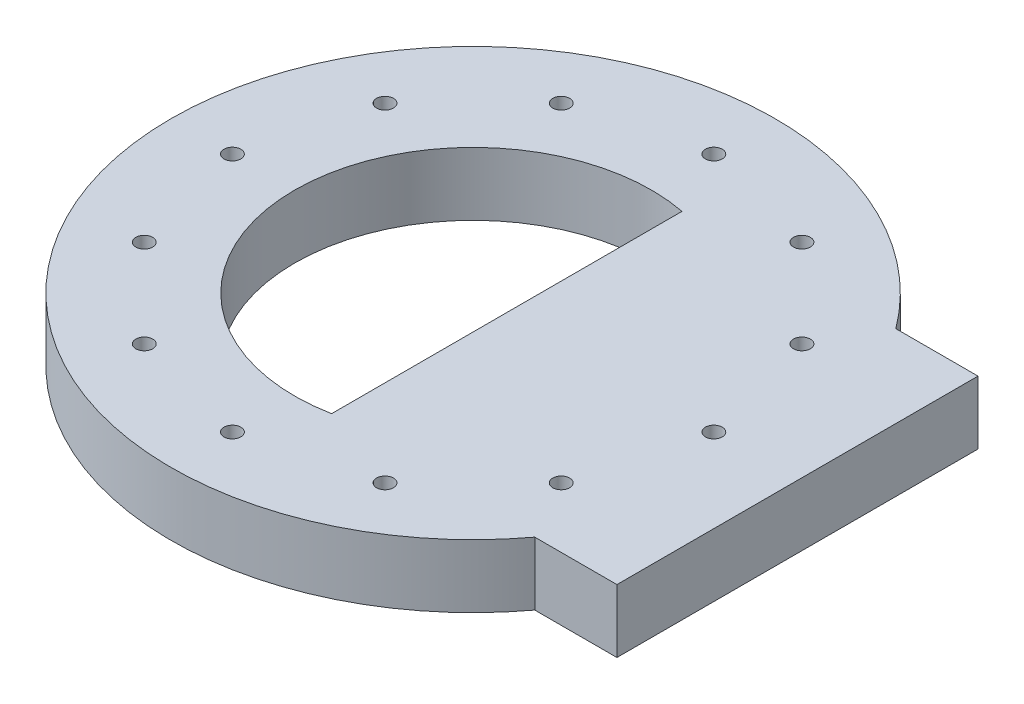
SolidWorks part; units mm, degrees
ref_plane "Front Plane" through (0, 0, 0) normal (0, 0, 1) x (1, 0, 0)
ref_plane "Top Plane" through (0, 0, 0) normal (0, 1, 0) x (1, 0, 0)
ref_plane "Right Plane" through (0, 0, 0) normal (1, 0, 0) x (0, 0, -1)
sketch "Sketch1" plane through (0, 0, 0) normal (0, 1, 0) x (1, 0, 0)
  circle A0 centre (0, 0) radius 101.6 construction
  circle A1 centre (0, 0) radius 127.508
  circle A2 centre (0, 0) radius 75.311
  circle A3 centre (0, 101.6) radius 3.5687
  circle A4 centre (50.8, 87.9882) radius 3.5687
  circle A5 centre (87.9882, 50.8) radius 3.5687
  circle A6 centre (101.6, 0) radius 3.5687
  circle A7 centre (87.9882, -50.8) radius 3.5687
  circle A8 centre (50.8, -87.9882) radius 3.5687
  circle A9 centre (0, -101.6) radius 3.5687
  circle A10 centre (-50.8, -87.9882) radius 3.5687
  circle A11 centre (-87.9882, -50.8) radius 3.5687
  circle A12 centre (-101.6, 0) radius 3.5687
  circle A13 centre (-87.9882, 50.8) radius 3.5687
  circle A14 centre (-50.8, 87.9882) radius 3.5687
  point P31 (0, 0)
  dimension "D1" = 203.2
  dimension "D2" = 255.016
  dimension "D4" = 7.1374
  dimension "D3" = 150.622
  dimension "D5" = 12
extrude "Boss-Extrude1" add sketch "Sketch1" along normal blind 26.67
sketch "Sketch2" plane through (0, 26.67, 0) normal (0, 1, 0) x (1, 0, 0)
  line L0 (14.224, 73.9556) -> (14.224, -73.9556)
  line L1 (136.906, 76.2) -> (136.906, -76.2)
  line L2 (136.906, 76.2) -> (102.2343, 76.2)
  line L3 (136.906, -76.2) -> (102.2343, -76.2)
  circle A0 centre (0, 0) radius 75.311 construction
  arc A1 (14.224, 73.9556) -> (14.224, -73.9556) centre (0, 0) cw
  circle A2 centre (0, 0) radius 127.508 construction
  arc A3 (102.2343, 76.2) -> (102.2343, -76.2) centre (0, 0) cw
  point P11 (136.906, 0)
  dimension "D1" = 14.224
  dimension "D2" = 136.906
  dimension "D3" = 152.4
extrude "Boss-Extrude2" add sketch "Sketch2" against normal through all
equation "\"A\"= 10.04in"
equation "\"B\"= 7in"
equation "\"C\"= 5.93in"
equation "\"D\"= .56in"
equation "\"E\"= 5.39in"
equation "\"F\"= 1.03in"
equation "\"D2@Sketch1\"=\"A\""
equation "\"BC\"=203.2"
equation "\"D1@Sketch1\"=\"BC\""
equation "\"diam_mount_hole\"=7.1374"
equation "\"D4@Sketch1\"=\"diam_mount_hole\""
equation "\"thick\"= 2.1in / 2"
equation "\"D1@Boss-Extrude1\"=\"thick\""
equation "\"D3@Sketch1\"=\"C\""
equation "\"D1@Sketch2\"=\"D\""
equation "\"D2@Sketch2\"=\"E\""
equation "\"D3@Sketch2\"=6in"
